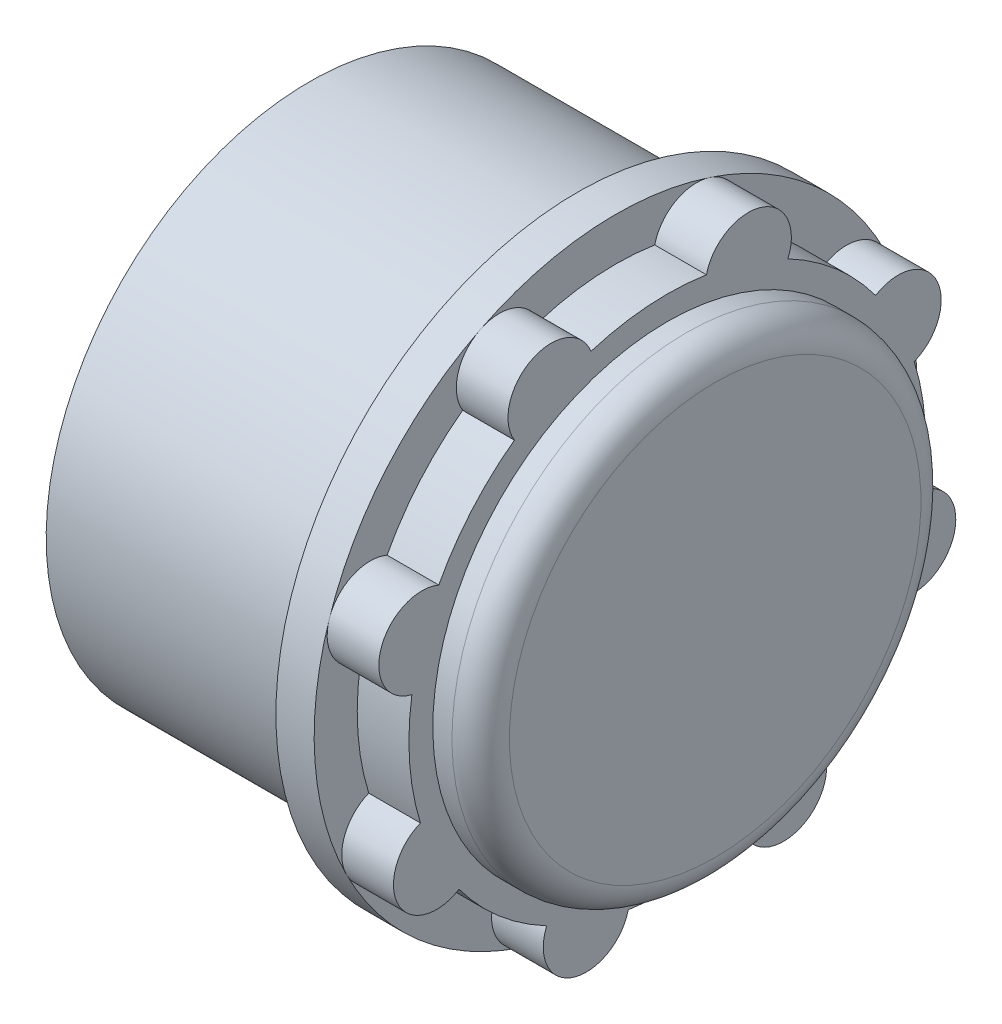
SolidWorks part; units mm, degrees
material "Nylon 101"
ref_plane "Front Plane" through (0, 0, 0) normal (0, 0, 1) x (1, 0, 0)
ref_plane "Top Plane" through (0, 0, 0) normal (0, 1, 0) x (1, 0, 0)
ref_plane "Right Plane" through (0, 0, 0) normal (1, 0, 0) x (0, 0, -1)
sketch "Sketch1" plane through (0, 0, 0) normal (1, 0, 0) x (0, 1, 0)
  circle A0 centre (0, 0) radius 15.75
  dimension "D1" = 31.5
extrude "Boss-Extrude1" add sketch "Sketch1" along normal blind 2
sketch "Sketch2" plane through (2, 0, 0) normal (1, 0, 0) x (0, 1, 0)
  arc A0 (10.8803, 7.9918) -> (6.301, 11.9393) centre (0, 0) ccw
  arc A1 (12.8978, 3.9869) -> (10.8803, 7.9918) centre (12.0565, 6.0737) ccw
  arc A2 (2.0425, 13.3446) -> (-3.9869, 12.8978) centre (0, 0) ccw
  arc A3 (-7.9918, 10.8803) -> (-11.9393, 6.301) centre (0, 0) ccw
  circle A4 centre (0, 0) radius 15.75 construction
  arc A5 (11.9393, -6.301) -> (13.3446, -2.0425) centre (12.82, -4.2305) ccw
  arc A6 (3.9869, -12.8978) -> (7.9918, -10.8803) centre (6.0737, -12.0565) ccw
  arc A7 (-6.301, -11.9393) -> (-2.0425, -13.3446) centre (-4.2305, -12.82) ccw
  arc A8 (-12.8978, -3.9869) -> (-10.8803, -7.9918) centre (-12.0565, -6.0737) ccw
  arc A9 (-11.9393, 6.301) -> (-13.3446, 2.0425) centre (-12.82, 4.2305) ccw
  arc A10 (-3.9869, 12.8978) -> (-7.9918, 10.8803) centre (-6.0737, 12.0565) ccw
  arc A11 (6.301, 11.9393) -> (2.0425, 13.3446) centre (4.2305, 12.82) ccw
  arc A12 (-13.3446, 2.0425) -> (-12.8978, -3.9869) centre (0, 0) ccw
  arc A13 (-10.8803, -7.9918) -> (-6.301, -11.9393) centre (0, 0) ccw
  arc A14 (-2.0425, -13.3446) -> (3.9869, -12.8978) centre (0, 0) ccw
  arc A15 (13.3446, -2.0425) -> (12.8978, 3.9869) centre (0, 0) ccw
  arc A16 (7.9918, -10.8803) -> (11.9393, -6.301) centre (0, 0) ccw
  point P24 (0, 0)
  dimension "D1" = 27
  dimension "D2" = 8
extrude "Boss-Extrude2" add sketch "Sketch2" along normal blind 2.7 contours A0 A11 A2 A10 A3 A9 A12 A8 A13 A7 A14 A6 A16 A5 A15 A1
sketch "Sketch3" plane through (4.7, 0, 0) normal (1, 0, 0) x (0, 1, 0)
  circle A0 centre (0, 0) radius 12.25
  dimension "D1" = 24.5
extrude "Boss-Extrude3" add sketch "Sketch3" along normal blind 2.5
sketch "Sketch4" plane through (0, 0, 0) normal (-1, 0, 0) x (0, -1, 0)
  circle A0 centre (0, 0) radius 13.75
  dimension "D1" = 27.5
extrude "Boss-Extrude4" add sketch "Sketch4" along normal blind 14 contours A0
cosmetic thread "Cosmetic Thread1" parameters "D2"=24.797
sketch "Sketch5" plane through (-14, 0, 0) normal (-1, 0, 0) x (0, -1, 0)
  circle A0 centre (0, 0) radius 11.25
  dimension "D1" = 22.5
extrude "Cut-Extrude1" cut sketch "Sketch5" against normal blind 20.5
fillet "Fillet1" radius 1.5 1 edges at (7.2, 12.25, 0)
fillet "Fillet2" radius 2 1 edges at (6.5, -11.25, 0)
